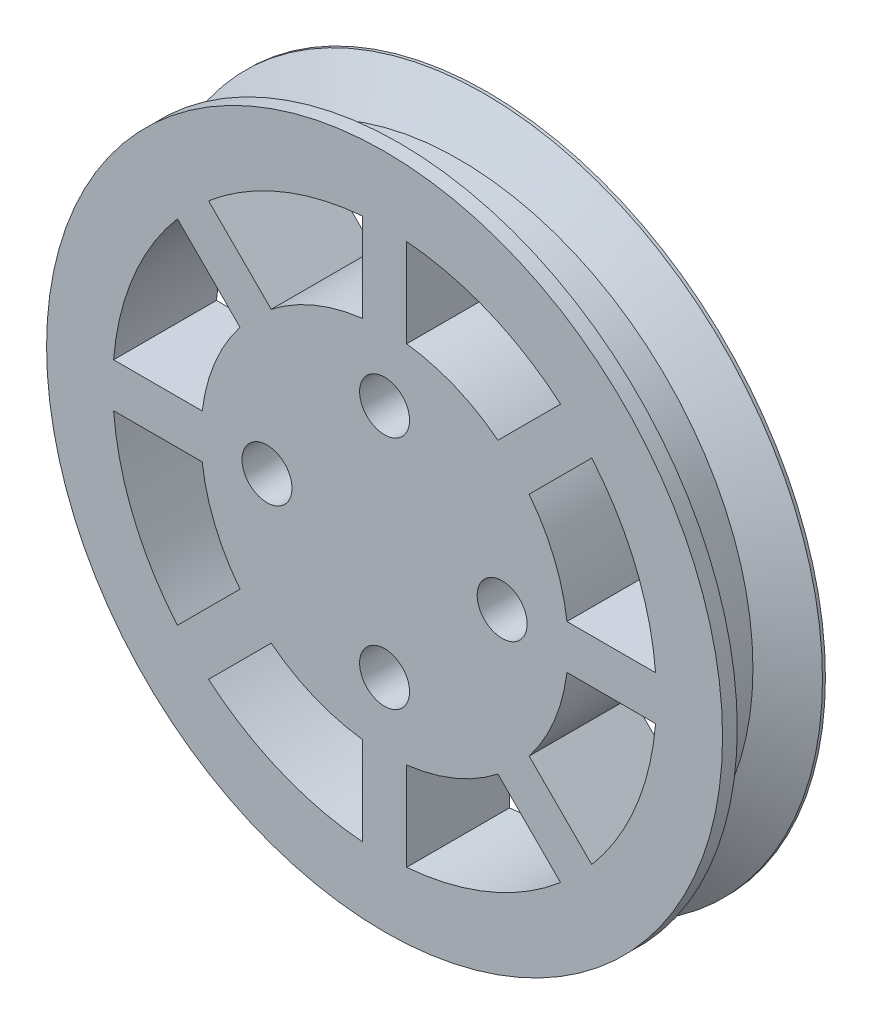
SolidWorks part; units mm, degrees
ref_plane "Front Plane" through (0, 0, 0) normal (0, 0, 1) x (1, 0, 0)
ref_plane "Top Plane" through (0, 0, 0) normal (0, 1, 0) x (1, 0, 0)
ref_plane "Right Plane" through (0, 0, 0) normal (1, 0, 0) x (0, 0, -1)
sketch "Sketch1" plane through (0, 0, 0) normal (0, 0, 1) x (1, 0, 0)
  circle A0 centre (0, 0) radius 20
  dimension "D1" = 40
extrude "Boss-Extrude1" add sketch "Sketch1" along normal mid plane 7
sketch "Sketch3" plane through (0, 0, 0) normal (0, 1, 0) x (1, 0, 0)
  line L0 (0, 3.5) -> (0, -3.5) construction
  line L1 (20, 3.5) -> (-20, 3.5) construction
  line L2 (-20, -3.5) -> (20, -3.5) construction
  line L3 (-20, 3.5) -> (-23, 3.5)
  line L4 (-23, 3.5) -> (-23, 3.3)
  line L5 (-23, 3.3) -> (-20, 1.5679)
  line L6 (-20, 3.5) -> (-20, -3.5) construction
  line L7 (-20, 1.5679) -> (-20, 3.5)
  point P9 (-20, 0.6924)
  point P14 (-21.1943, 1.9)
  dimension "D1" = 0.2
  dimension "D2" = 60
  dimension "D3" = 3
revolve "Revolve1" add sketch "Sketch3" angle 360 about L0
sketch "Sketch4" plane through (0, 0, 3.5) normal (0, 0, 1) x (1, 0, 0)
  circle A0 centre (0, 0) radius 23 construction
  circle A1 centre (0, 0) radius 23
extrude "Boss-Extrude2" add sketch "Sketch4" against normal blind 1
fillet "Fillet1" radius 1 1 edges at (20, 0, 2.5)
sketch "Sketch5" plane through (0, 0, -3.5) normal (0, 0, -1) x (-1, 0, 0)
  circle A0 centre (0, 0) radius 8 construction
  circle A1 centre (0, 8) radius 1.5
  circle A2 centre (8, 0) radius 1.5
  circle A3 centre (0, -8) radius 1.5
  circle A4 centre (-8, 0) radius 1.5
  point P2 (0, 0)
  point P6 (0, 0)
  point P14 (0, 0)
  dimension "D1" = 16
  dimension "D2" = 3
  dimension "D3" = 4
hole_wizard "CSK for M3 Flat Head Machine Screw1" positions "Sketch6" profile "Sketch7" countersink size "M3" standard "ANSI Metric"
sketch "Sketch6" plane through (0, 0, -3.5) normal (0, 0, -1) x (-1, 0, 0)
  point P0 (0, 8)
  point P3 (-8, 0)
  point P6 (0, -8)
  point P9 (8, 0)
sketch "Sketch7" plane through (0, 8, -3.5) normal (1, 0, 0) x (0, 1, 0)
  line L0 (0, 0) -> (0, 8.0215)
  line L1 (0, 8.0215) -> (1.7, 7)
  line L2 (1.7, 7) -> (1.7, 1.45)
  line L3 (1.7, 1.45) -> (3.15, 0)
  line L5 (3.15, 0) -> (0, 0)
  line L6 (-1.7, 1.45) -> (-3.15, 0) construction
  line L10 (0, 8.0215) -> (-1.7, 7) construction
  line L11 (0, -6.35) -> (0, 107.95) construction
  dimension "Hole Dia." = 3.4
  dimension "Hole Depth" = 7
  dimension "Near C'Sink Dia." = 6.3
  dimension "Near C'Sink Angle" = 90
  dimension "Drill Angle" = 118
sketch "Sketch8" plane through (0, 0, -3.5) normal (0, 0, -1) x (-1, 0, 0)
  line L0 (0, 0) -> (0, 23) construction
  line L1 (0, 0) -> (-16.2635, 16.2635) construction
  line L2 (0, 0) -> (-8.8017, 21.2492) construction
  line L3 (-1.5, 18.4391) -> (-1.5, 12.4097)
  line L4 (-11.9777, 14.0991) -> (-7.7143, 9.8356)
  line L5 (1.5, 18.4391) -> (1.5, 12.4097)
  line L6 (11.9777, 14.0991) -> (7.7143, 9.8356)
  line L7 (14.0991, 11.9777) -> (9.8356, 7.7143)
  line L8 (18.4391, 1.5) -> (12.4097, 1.5)
  line L9 (18.4391, -1.5) -> (12.4097, -1.5)
  line L10 (14.0991, -11.9777) -> (9.8356, -7.7143)
  line L11 (11.9777, -14.0991) -> (7.7143, -9.8356)
  line L12 (1.5, -18.4391) -> (1.5, -12.4097)
  line L13 (-1.5, -18.4391) -> (-1.5, -12.4097)
  line L14 (-11.9777, -14.0991) -> (-7.7143, -9.8356)
  line L15 (-14.0991, -11.9777) -> (-9.8356, -7.7143)
  line L16 (-18.4391, -1.5) -> (-12.4097, -1.5)
  line L17 (-18.4391, 1.5) -> (-12.4097, 1.5)
  line L18 (-14.0991, 11.9777) -> (-9.8356, 7.7143)
  circle A0 centre (0, 0) radius 23 construction
  arc A1 (-1.5, 18.4391) -> (-11.9777, 14.0991) centre (0, 0) ccw
  arc A2 (-1.5, 12.4097) -> (-7.7143, 9.8356) centre (0, 0) ccw
  circle A3 centre (0, 0) radius 20 construction
  circle A4 centre (0, 0) radius 20 construction
  arc A5 (7.7143, 9.8356) -> (1.5, 12.4097) centre (0, 0) ccw
  arc A6 (11.9777, 14.0991) -> (1.5, 18.4391) centre (0, 0) ccw
  arc A7 (12.4097, 1.5) -> (9.8356, 7.7143) centre (0, 0) ccw
  arc A8 (18.4391, 1.5) -> (14.0991, 11.9777) centre (0, 0) ccw
  arc A9 (9.8356, -7.7143) -> (12.4097, -1.5) centre (0, 0) ccw
  arc A10 (14.0991, -11.9777) -> (18.4391, -1.5) centre (0, 0) ccw
  arc A11 (1.5, -12.4097) -> (7.7143, -9.8356) centre (0, 0) ccw
  arc A12 (1.5, -18.4391) -> (11.9777, -14.0991) centre (0, 0) ccw
  arc A13 (-7.7143, -9.8356) -> (-1.5, -12.4097) centre (0, 0) ccw
  arc A14 (-11.9777, -14.0991) -> (-1.5, -18.4391) centre (0, 0) ccw
  arc A15 (-12.4097, -1.5) -> (-9.8356, -7.7143) centre (0, 0) ccw
  arc A16 (-18.4391, -1.5) -> (-14.0991, -11.9777) centre (0, 0) ccw
  arc A17 (-9.8356, 7.7143) -> (-12.4097, 1.5) centre (0, 0) ccw
  arc A18 (-14.0991, 11.9777) -> (-18.4391, 1.5) centre (0, 0) ccw
  point P46 (0, 0)
  dimension "D4" = 12.5
  dimension "D5" = 1.5
  dimension "D1" = 45
  dimension "D2" = 22.5
  dimension "D3" = 1.5
  dimension "D6" = 8
extrude "Cut-Extrude1" cut sketch "Sketch8" against normal through all
